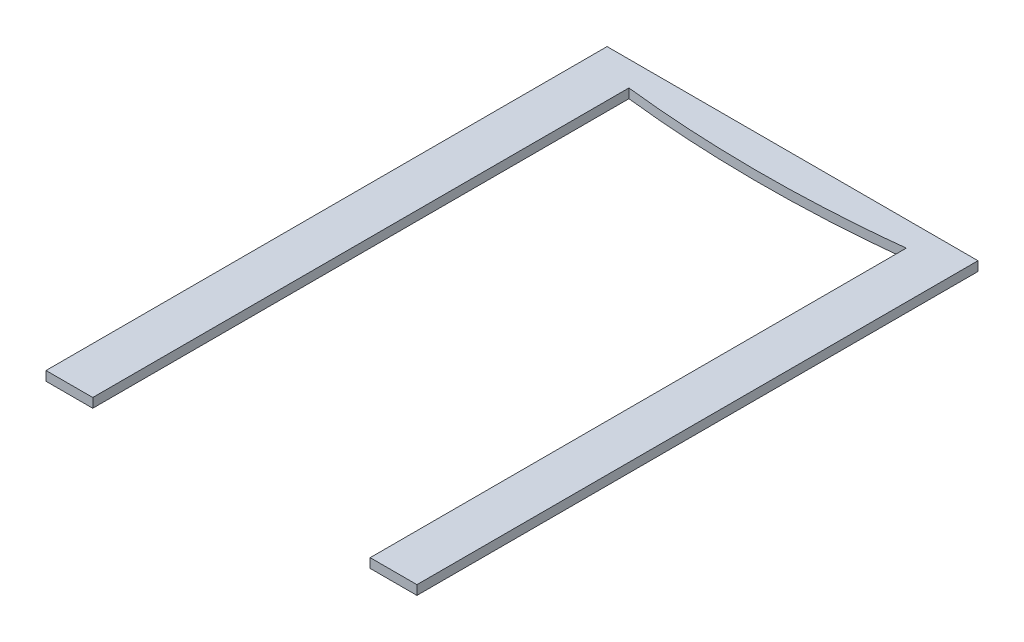
SolidWorks part; units mm, degrees
ref_plane "Front" through (0, 0, 0) normal (0, 0, 1) x (1, 0, 0)
ref_plane "Top" through (0, 0, 0) normal (0, 1, 0) x (1, 0, 0)
ref_plane "Right" through (0, 0, 0) normal (1, 0, 0) x (0, 0, -1)
sketch "Sketch1" plane through (0, 0, 0) normal (0, 1, 0) x (1, 0, 0)
  line L0 (-59.5, -90) -> (-59.5, 90)
  line L1 (-59.5, 90) -> (59.5, 90)
  line L2 (59.5, 90) -> (59.5, -90)
  line L3 (59.5, -90) -> (44.5, -90)
  line L4 (44.5, -90) -> (44.5, 82)
  line L5 (-44.5, 82) -> (0, 77) construction
  line L6 (-44.5, 82) -> (-44.5, -90)
  line L7 (-44.5, -90) -> (-59.5, -90)
  line L8 (0, 77) -> (44.5, 82) construction
  line L9 (0, 365.7396) -> (0, -18.836) construction
  line L10 (-50, 0) -> (50, 0) construction
  line L11 (0, -50) -> (0, 50) construction
  spline S0 degree 2 poles (-44.5, 82) (0, 77) (44.5, 82) knots 0 0 0 1 1 1
  point P2 (59.5, 0)
  point P13 (0, 90)
  dimension "D1" = 15
  dimension "D2" = 15
  dimension "D3" = 8
  dimension "D4" = 180
  dimension "D5" = 5
  dimension "D6" = 89
extrude "Boss-Extrude1" add sketch "Sketch1" along normal blind 3
sketch "Sketch2" plane through (0, 3, 0) normal (0, 1, 0) x (1, 0, 0)
  line L0 (0, -850) -> (0, 49150) construction
  line L1 (59.5, 90) -> (-59.5, 90) construction
  point P5 (0, 90)
equation "\"gripper-grip-height\"=3"
equation "\"D1@Boss-Extrude1\"=\"gripper-grip-height\""
equation "\"D6@Sketch1\"=104.00-\"D1@Sketch1\""
equation "\"D2@Sketch1\"=\"D1@Sketch1\""
